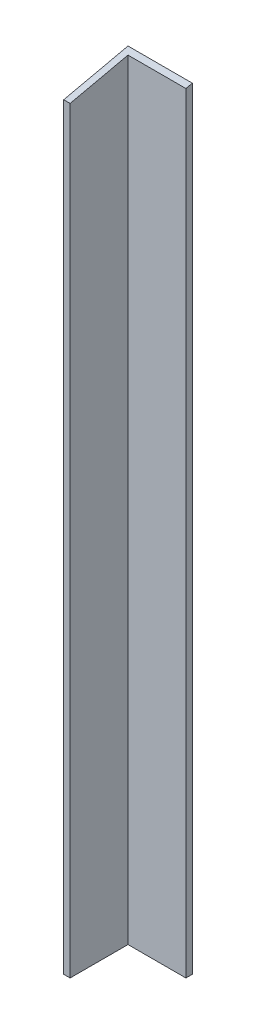
SolidWorks part; units mm, degrees
material "AISI 1020"
ref_plane "Front Plane" through (0, 0, 0) normal (0, 0, 1) x (1, 0, 0)
ref_plane "Top Plane" through (0, 0, 0) normal (0, 1, 0) x (1, 0, 0)
ref_plane "Right Plane" through (0, 0, 0) normal (1, 0, 0) x (0, 0, -1)
sketch "Sketch1" plane through (0, 0, 0) normal (0, 0, 1) x (1, 0, 0)
  line L1 (-61.4627, 118.1642) -> (-41.4627, 118.1642)
  line L2 (-61.4627, 118.1642) -> (-61.4627, -121.8358)
  line L3 (-61.4627, -121.8358) -> (-41.4627, -121.8358)
  line L4 (-41.4627, 118.1642) -> (-41.4627, -121.8358)
  dimension "D1" = 240
  dimension "D2" = 20
extrude "Boss-Extrude1" add sketch "Sketch1" against normal blind 20
sketch "Sketch2" plane through (-61.4627, 0, 0) normal (-1, 0, 0) x (0, 0, 1)
  line L0 (-20, 118.1642) -> (0, 113.6936)
  line L1 (0, 118.1642) -> (0, -121.8358) construction
  line L2 (0, 113.6936) -> (0, 118.1642)
  line L3 (0, 118.1642) -> (-20, 118.1642)
extrude "Cut-Extrude1" cut sketch "Sketch2" against normal blind 20
sketch "Sketch3" plane through (0, -121.8358, 0) normal (0, -1, 0) x (1, 0, 0)
  line L5 (-41.4627, 0) -> (-59.4627, 0)
  line L6 (-41.4627, 0) -> (-41.4627, -18)
  line L7 (-41.4627, -18) -> (-59.4627, -18)
  line L8 (-59.4627, 0) -> (-59.4627, -18)
  dimension "D1" = 18
  dimension "D2" = 18
extrude "Cut-Extrude2" cut sketch "Sketch3" against normal blind 290
